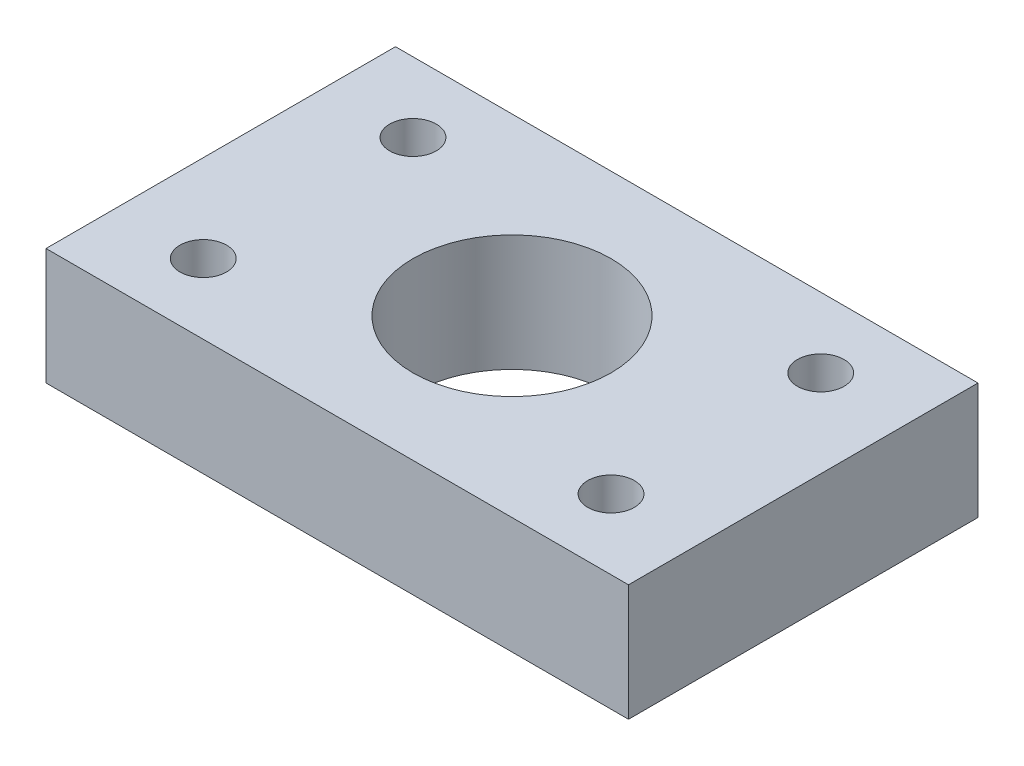
SolidWorks part; units mm, degrees
ref_plane "Front Plane" through (0, 0, 0) normal (0, 0, 1) x (1, 0, 0)
ref_plane "Top Plane" through (0, 0, 0) normal (0, 1, 0) x (1, 0, 0)
ref_plane "Right Plane" through (0, 0, 0) normal (1, 0, 0) x (0, 0, -1)
sketch "Sketch1" plane through (0, 0, 0) normal (0, 1, 0) x (1, 0, 0)
  line L0 (0, 15) -> (0, 0) construction
  line L1 (25, -15) -> (-25, -15)
  line L2 (25, -15) -> (25, 15)
  line L3 (25, 15) -> (-25, 15)
  line L4 (-25, -15) -> (-25, 15)
  line L5 (25, -15) -> (-25, 15) construction
  line L6 (25, 15) -> (-25, -15) construction
  line L7 (0, 0) -> (-25, 0) construction
  circle A0 centre (0, 0) radius 8.5
  circle A1 centre (-17.5, 9) radius 2
  circle A2 centre (17.5, 9) radius 2
  circle A3 centre (17.5, -9) radius 2
  circle A4 centre (-17.5, -9) radius 2
  point P0 (0, 0)
  dimension "D1" = 17
  dimension "D6" = 4
  dimension "D2" = 30
  dimension "D3" = 50
  dimension "D4" = 18
  dimension "D5" = 35
extrude "Boss-Extrude1" add sketch "Sketch1" along normal blind 10
